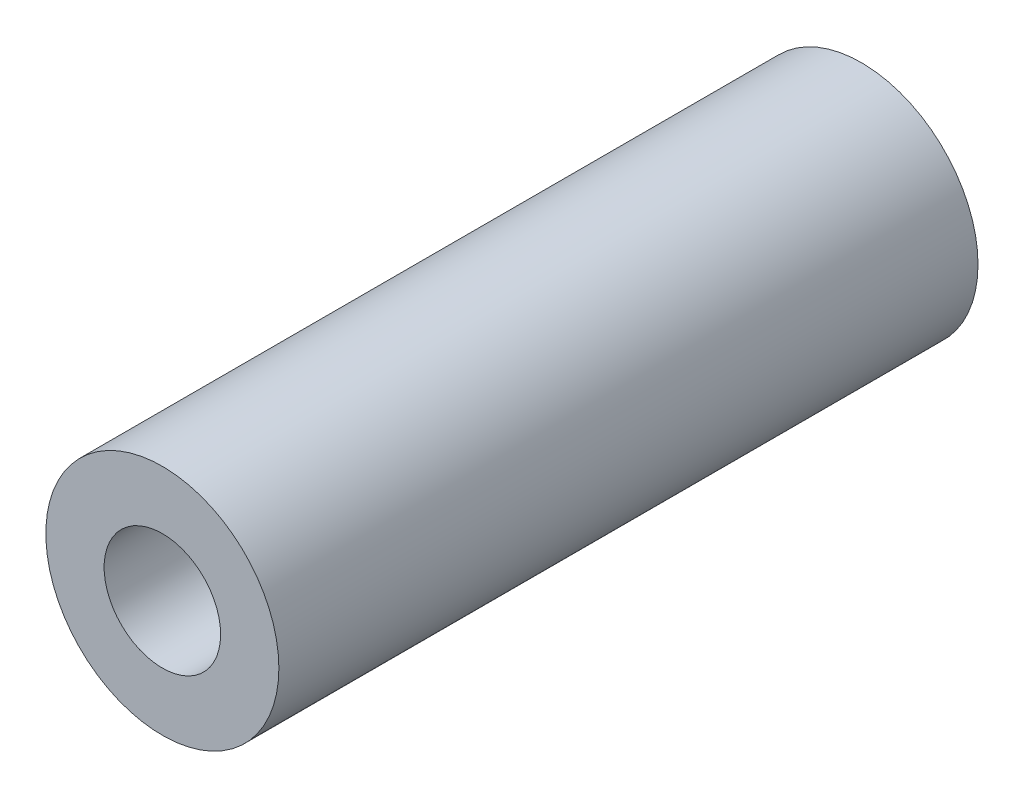
SolidWorks part; units mm, degrees
ref_plane "Front Plane" through (0, 0, 0) normal (0, 0, 1) x (1, 0, 0)
ref_plane "Top Plane" through (0, 0, 0) normal (0, 1, 0) x (1, 0, 0)
ref_plane "Right Plane" through (0, 0, 0) normal (1, 0, 0) x (0, 0, -1)
sketch "Sketch1" plane through (0, 0, 0) normal (0, 0, 1) x (1, 0, 0)
  circle A0 centre (0, 0) radius 20
  circle A1 centre (0, 0) radius 10
  point P0 (0, 0)
  point P4 (0, 0)
  dimension "D1" = 40
  dimension "D2" = 20
extrude "Boss-Extrude1" add sketch "Sketch1" along normal blind 120
